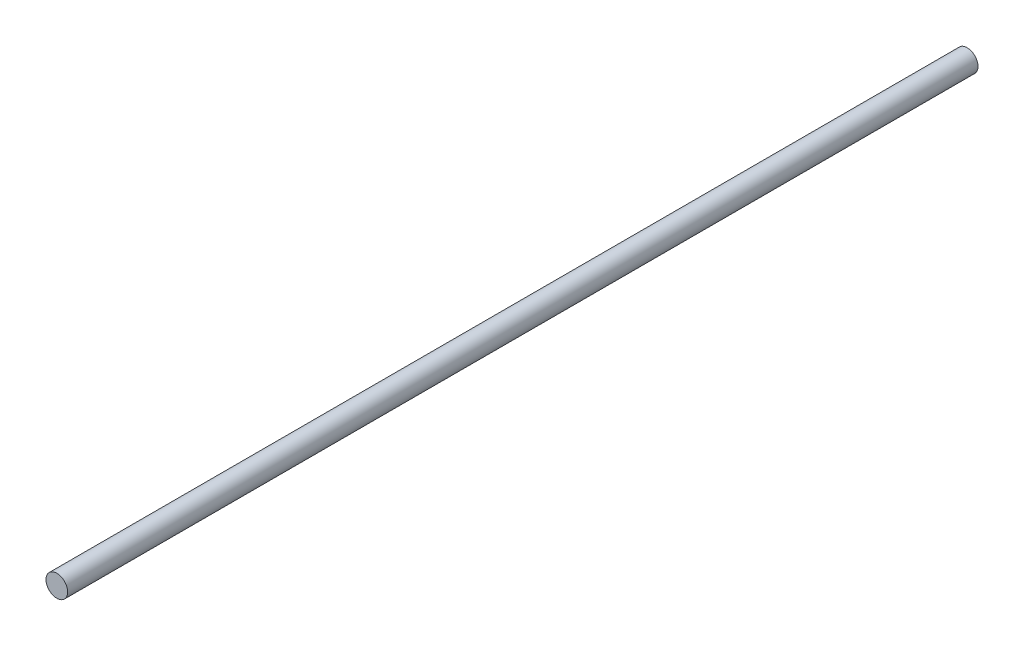
SolidWorks part; units mm, degrees
ref_plane "Front Plane" through (0, 0, 0) normal (0, 0, 1) x (1, 0, 0)
ref_plane "Top Plane" through (0, 0, 0) normal (0, 1, 0) x (1, 0, 0)
ref_plane "Right Plane" through (0, 0, 0) normal (1, 0, 0) x (0, 0, -1)
sketch "Sketch1" plane through (0, 0, 0) normal (0, 0, 1) x (1, 0, 0)
  circle A0 centre (0, 0) radius 5
  dimension "D1" = 10
extrude "Boss-Extrude1" add sketch "Sketch1" along normal blind 420
